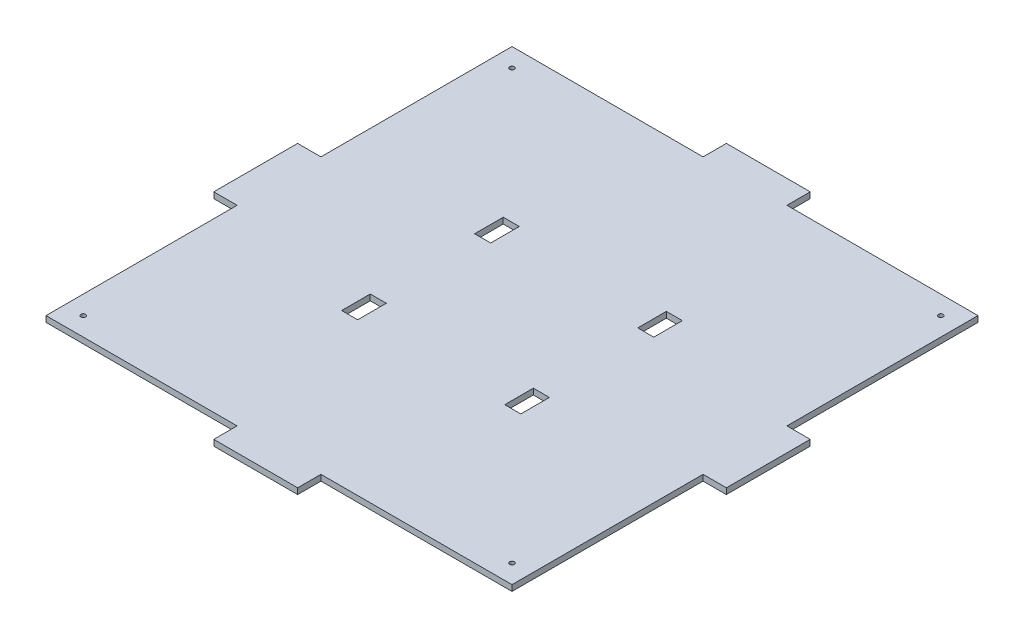
SolidWorks part; units mm, degrees
ref_plane "Front Plane" through (0, 0, 0) normal (0, 0, 1) x (1, 0, 0)
ref_plane "Top Plane" through (0, 0, 0) normal (0, 1, 0) x (1, 0, 0)
ref_plane "Right Plane" through (0, 0, 0) normal (1, 0, 0) x (0, 0, -1)
sketch "Sketch2" plane through (0, 0, 0) normal (0, 1, 0) x (1, 0, 0)
  line L1 (-125, -125) -> (125, -125)
  line L2 (-125, -125) -> (-125, 125)
  line L3 (-125, 125) -> (125, 125)
  line L4 (125, -125) -> (125, 125)
  line L5 (-125, -125) -> (125, 125) construction
  line L6 (-125, 125) -> (125, -125) construction
  point P0 (0, 0)
  dimension "250" = 250
extrude "Base" add sketch "Sketch2" along normal blind 3.175
sketch "Sketch3" plane through (0, 3.175, 0) normal (0, 1, 0) x (1, 0, 0)
  line L0 (-125, 0) -> (125, 0) construction
  line L1 (-125, 125) -> (-125, -125) construction
  line L2 (125, -125) -> (125, 125) construction
  line L3 (-43.75, 125) -> (-43.75, -125) construction
  line L4 (125, 125) -> (-125, 125) construction
  line L5 (-125, -125) -> (125, -125) construction
  line L6 (0, 125) -> (0, -125) construction
  line L11 (-48.05, 28) -> (-39.45, 28)
  line L12 (-48.05, 28) -> (-48.05, 43.35)
  line L13 (-48.05, 43.35) -> (-39.45, 43.35)
  line L14 (-39.45, 28) -> (-39.45, 43.35)
  line L15 (-48.05, 28) -> (-39.45, 43.35) construction
  line L16 (-48.05, 43.35) -> (-39.45, 28) construction
  line L21 (-48.05, -43.35) -> (-39.45, -43.35)
  line L22 (-48.05, -43.35) -> (-48.05, -28)
  line L23 (-48.05, -28) -> (-39.45, -28)
  line L24 (-39.45, -43.35) -> (-39.45, -28)
  line L25 (-48.05, -43.35) -> (-39.45, -28) construction
  line L26 (-48.05, -28) -> (-39.45, -43.35) construction
  line L27 (48.05, -28) -> (39.45, -28)
  line L28 (39.45, -43.35) -> (39.45, -28)
  line L29 (48.05, -43.35) -> (39.45, -43.35)
  line L30 (48.05, -43.35) -> (48.05, -28)
  line L31 (48.05, 43.35) -> (39.45, 43.35)
  line L32 (39.45, 28) -> (39.45, 43.35)
  line L33 (48.05, 28) -> (39.45, 28)
  line L34 (48.05, 28) -> (48.05, 43.35)
  point P12 (-43.75, 35.675)
  point P17 (-43.75, -35.675)
  dimension "D1" = 43.75
  dimension "D2" = 8.6
  dimension "D3" = 15.35
  dimension "D4" = 56
  dimension "D5" = 28
extrude "Holes" cut sketch "Sketch3" against normal blind 10
sketch "Sketch10" plane through (0, 0, -125) normal (0, 0, -1) x (-1, 0, 0)
  line L0 (-125, 1.5875) -> (125, 1.5875) construction
  line L1 (-125, 3.175) -> (-125, 0) construction
  line L2 (125, 3.175) -> (125, 0) construction
  line L8 (-125, 3.175) -> (125, 3.175) construction
  line L9 (-22.5, 0) -> (22.5, 0)
  line L10 (-22.5, 0) -> (-22.5, 3.175)
  line L11 (-22.5, 3.175) -> (22.5, 3.175)
  line L12 (22.5, 0) -> (22.5, 3.175)
  line L13 (-22.5, 0) -> (22.5, 3.175) construction
  line L14 (-22.5, 3.175) -> (22.5, 0) construction
  point P6 (0, 1.5875)
  dimension "D1" = 45
extrude "Jigsaw1" add sketch "Sketch10" along normal blind 12.5
sketch "Sketch11" plane through (-125, 0, 0) normal (-1, 0, 0) x (0, 0, 1)
  line L0 (-125, 1.5875) -> (125, 1.5875) construction
  line L1 (-125, 3.175) -> (-125, 0) construction
  line L2 (125, 3.175) -> (125, 0) construction
  line L9 (-22.5, 0) -> (22.5, 0)
  line L10 (-22.5, 0) -> (-22.5, 3.175)
  line L11 (-22.5, 3.175) -> (22.5, 3.175)
  line L12 (22.5, 0) -> (22.5, 3.175)
  line L13 (-22.5, 0) -> (22.5, 3.175) construction
  line L14 (-22.5, 3.175) -> (22.5, 0) construction
  point P6 (0, 1.5875)
  dimension "D1" = 45
  dimension "D2" = 3.175
extrude "Jigsaw2" add sketch "Sketch11" along normal blind 12.5
sketch "Sketch13" plane through (0, 0, 125) normal (0, 0, 1) x (1, 0, 0)
  line L0 (-125, 1.5875) -> (125, 1.5875) construction
  line L3 (-125, 0) -> (-125, 3.175) construction
  line L9 (-22.5, 0) -> (22.5, 0)
  line L10 (-22.5, 0) -> (-22.5, 3.175)
  line L11 (-22.5, 3.175) -> (22.5, 3.175)
  line L12 (22.5, 0) -> (22.5, 3.175)
  line L13 (-22.5, 0) -> (22.5, 3.175) construction
  line L14 (-22.5, 3.175) -> (22.5, 0) construction
  line L15 (125, 3.175) -> (125, 0) construction
  point P6 (0, 1.5875)
  dimension "D1" = 45
  dimension "D2" = 3.175
extrude "Jigsaw3" add sketch "Sketch13" along normal blind 12.5
sketch "Sketch14" plane through (125, 0, 0) normal (1, 0, 0) x (0, 0, -1)
  line L0 (-125, 1.5875) -> (125, 1.5875) construction
  line L3 (-125, 3.175) -> (-125, 0) construction
  line L9 (-22.5, 0) -> (22.5, 0)
  line L10 (-22.5, 0) -> (-22.5, 3.175)
  line L11 (-22.5, 3.175) -> (22.5, 3.175)
  line L12 (22.5, 0) -> (22.5, 3.175)
  line L13 (-22.5, 0) -> (22.5, 3.175) construction
  line L14 (-22.5, 3.175) -> (22.5, 0) construction
  line L15 (125, 3.175) -> (125, 0) construction
  point P6 (0, 1.5875)
  dimension "D1" = 45
  dimension "D2" = 3.175
extrude "Jigsaw4" add sketch "Sketch14" along normal blind 12.5
hole_wizard "Standoff Holes" positions "3DSketch4" profile "Sketch20" tap size "M3" standard "ISO" end condition through all
sketch3d "3DSketch4"
  line L0 (-22.5, 3.175, -125) -> (-125, 3.175, -125) construction
  line L1 (-125, 3.175, -125) -> (-125, 3.175, -22.5) construction
  point P0 (-115, 3.175, -115)
  dimension "D1" = 10
  dimension "D2" = 10
sketch "Sketch20" plane through (-115, 3.175, -115) normal (1, 0, 0) x (0, 0, 1)
  line L0 (0, 0) -> (0, 3.175)
  line L1 (0, 3.175) -> (1.25, 3.175)
  line L2 (1.25, 3.175) -> (1.25, 0)
  line L5 (1.25, 0) -> (0, 0)
  line L11 (0, -6.35) -> (0, 107.95) construction
  dimension "Thru Tap Drill Dia." = 2.5
  dimension "Thru Tap Drill Depth" = 3.175
cosmetic thread "Hole Thread1" parameters "D2"=3
sketch "Sketch21" plane through (0, 3.175, 0) normal (0, 1, 0) x (1, 0, 0)
  line L0 (0, -137.5) -> (0, 137.5)
  line L1 (22.5, -137.5) -> (-22.5, -137.5) construction
  line L2 (-22.5, 137.5) -> (22.5, 137.5) construction
  line L3 (-137.5, 0) -> (137.5, 0)
  line L4 (-137.5, -22.5) -> (-137.5, 22.5) construction
  line L5 (137.5, 22.5) -> (137.5, -22.5) construction
  circle A0 centre (-115, 115) radius 1.25
  circle A1 centre (115, 115) radius 1.25
  circle A2 centre (115, -115) radius 1.25
  circle A3 centre (-115, -115) radius 1.25
extrude "Standoff Holes 2" cut sketch "Sketch21" against normal blind 10 contours A1 | A2 | A3
